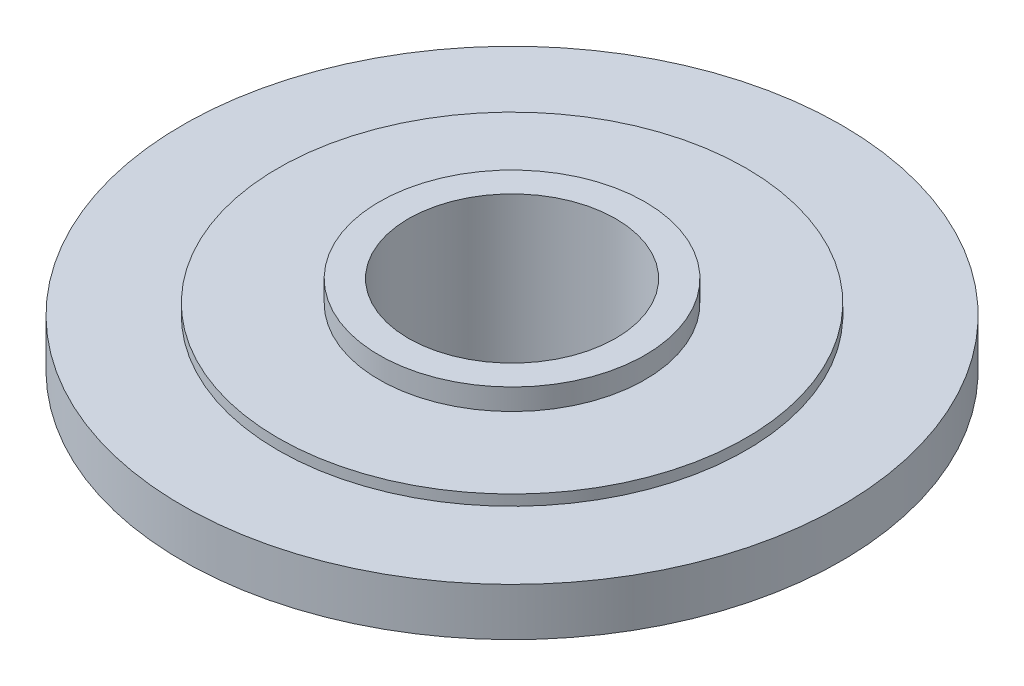
SolidWorks part; units mm, degrees
ref_plane "Front Plane" through (0, 0, 0) normal (0, 0, 1) x (1, 0, 0)
ref_plane "Top Plane" through (0, 0, 0) normal (0, 1, 0) x (1, 0, 0)
ref_plane "Right Plane" through (0, 0, 0) normal (1, 0, 0) x (0, 0, -1)
sketch "Sketch2" plane through (0, 0, 0) normal (0, 0, 1) x (1, 0, 0)
  line L0 (0, 38) -> (0, 20) construction
  line L1 (0, 0) -> (26, 0)
  line L2 (26, 0) -> (26, 20)
  line L3 (0, 20) -> (0, 0) construction
  line L4 (0, 0) -> (0, 38)
  line L5 (30.5, 23) -> (62, 23)
  line L6 (62, 23) -> (62, 32)
  line L7 (62, 32) -> (44, 32)
  line L9 (25, 34) -> (44, 34)
  line L10 (44, 34) -> (44, 32)
  line L11 (0, 38) -> (25, 38)
  line L12 (25, 38) -> (25, 34)
  line L13 (26, 20) -> (30.5, 20)
  line L14 (30.5, 20) -> (30.5, 23)
  point P0 (34.9942, 18.249)
  dimension "D1" = 62
  dimension "D2" = 26
  dimension "D3" = 25
  dimension "D4" = 26
  dimension "D5" = 30.5
  dimension "D6" = 38
  dimension "D7" = 3
  dimension "D8" = 9
  dimension "D9" = 2
  dimension "D10" = 20
  dimension "D11" = 4
  dimension "D12" = 2
  dimension "D13" = 88
revolve "Revolve1" add sketch "Sketch2" angle 360 about L4
sketch "Sketch3" plane through (0, 38, 0) normal (0, 1, 0) x (1, 0, 0)
  circle A0 centre (0, 0) radius 19.5
  dimension "D1" = 39
extrude "Cut-Extrude1" cut sketch "Sketch3" against normal blind 50
